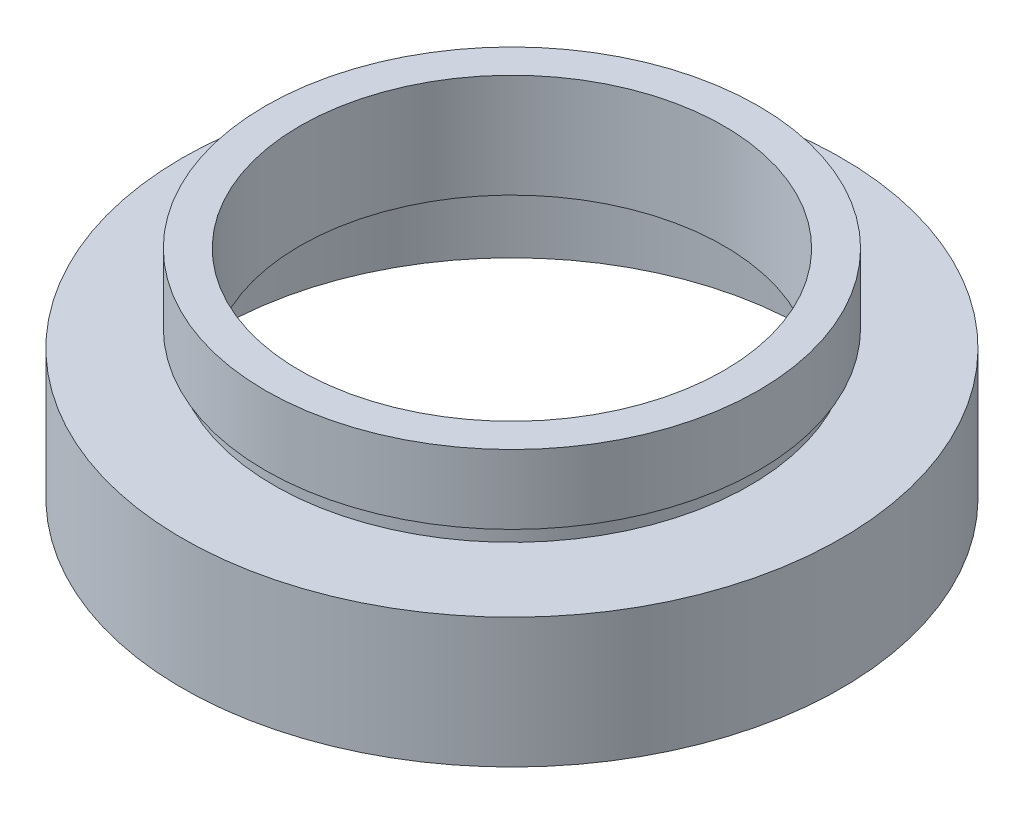
SolidWorks part; units mm, degrees
ref_plane "前视基准面" through (0, 0, 0) normal (0, 0, 1) x (1, 0, 0)
ref_plane "上视基准面" through (0, 0, 0) normal (0, 1, 0) x (1, 0, 0)
ref_plane "右视基准面" through (0, 0, 0) normal (1, 0, 0) x (0, 0, -1)
sketch "草图1" plane through (0, 0, 0) normal (0, 0, 1) x (1, 0, 0)
  line L0 (0, 16.886) -> (0, -24.4878) construction
  line L1 (17, 0) -> (17, 5.5)
  line L2 (12.25, 6.5) -> (17.6, 6.5)
  line L3 (12.25, 6.5) -> (12.25, 12.5)
  line L4 (12.25, 12.5) -> (14.25, 12.5)
  line L5 (14.25, 12.5) -> (14.25, 8.5)
  line L6 (14.25, 8.5) -> (13.75, 8.5)
  line L7 (13.75, 8.5) -> (13.75, 7.5)
  line L8 (13.75, 7.5) -> (19.05, 7.5)
  line L9 (19.05, 7.5) -> (19.05, 0)
  line L10 (19.05, 0) -> (17, 0)
  line L11 (17, 5.5) -> (17.6, 5.5)
  line L12 (17.6, 5.5) -> (17.6, 6.5)
  line L13 (0, 0) -> (3.4668, 0) construction
  point P4 (18.025, 0)
  dimension "D1" = 12.25
  dimension "D2" = 14.25
  dimension "D3" = 13.75
  dimension "D4" = 17
  dimension "D5" = 17.6
  dimension "D6" = 19.05
  dimension "D7" = 12.5
  dimension "D8" = 7.5
  dimension "D9" = 1
  dimension "D10" = 5.5
  dimension "D11" = 1
revolve "旋转1" add sketch "草图1" angle 360 about L0
cosmetic thread "装饰螺纹线1" parameters "D2"=27.5
cosmetic thread "装饰螺纹线2" parameters "D2"=25.5
cosmetic thread "装饰螺纹线3" parameters "D2"=35
